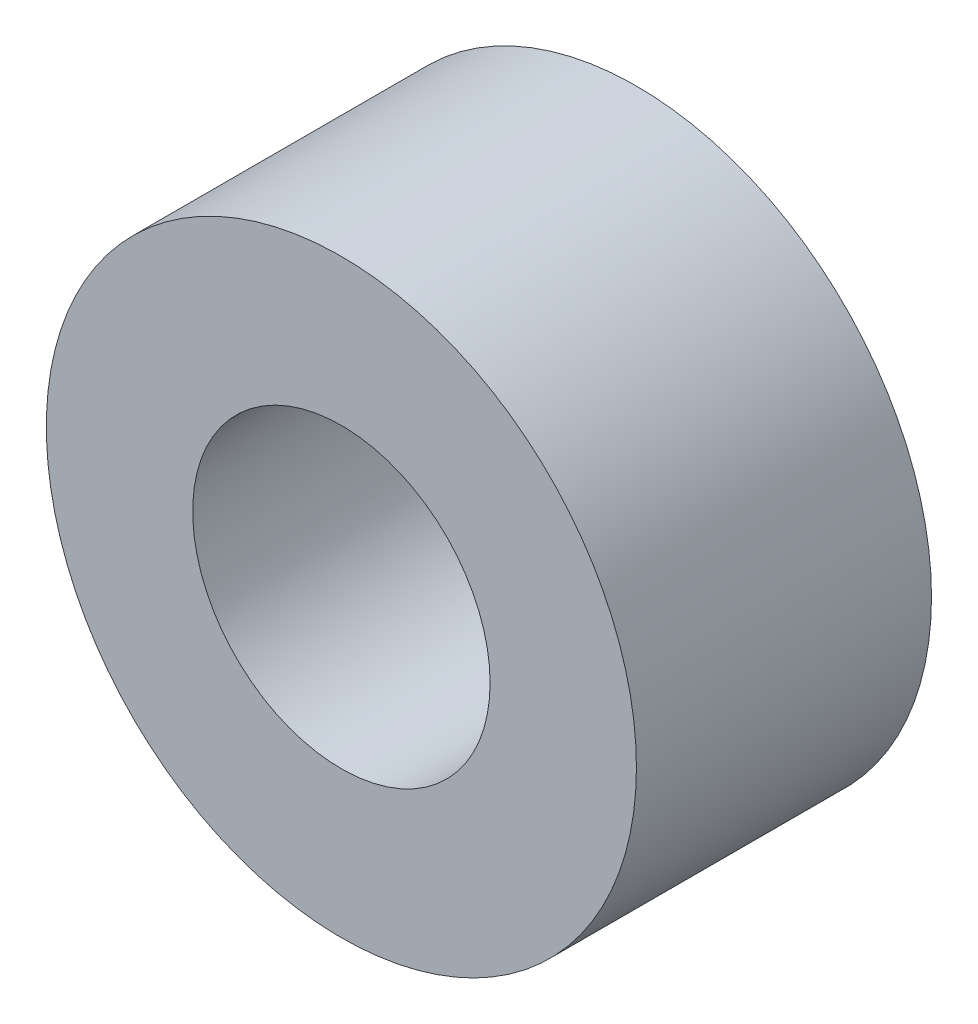
SolidWorks part; units mm, degrees
ref_plane "Front Plane" through (0, 0, 0) normal (0, 0, 1) x (1, 0, 0)
ref_plane "Top Plane" through (0, 0, 0) normal (0, 1, 0) x (1, 0, 0)
ref_plane "Right Plane" through (0, 0, 0) normal (1, 0, 0) x (0, 0, -1)
sketch "Sketch1" plane through (0, 0, 0) normal (0, 0, 1) x (1, 0, 0)
  circle A0 centre (0, 0) radius 6.35
  circle A1 centre (0, 0) radius 3.2004
  dimension "OD" = 12.7
  dimension "ID" = 6.4008
extrude "Extrude1" add sketch "Sketch1" along normal mid plane 6.35
sketch "Sketch2" plane through (0, 0, 0) normal (1, 0, 0) x (0, 0, -1)
  line L0 (-3.175, -3.2004) -> (3.175, -3.2004) construction
  line L3 (3.175, 3.2004) -> (-3.175, 3.2004) construction
  line L5 (-3.175, -3.2004) -> (3.175, -3.2004)
  line L6 (3.175, 3.2004) -> (-3.175, 3.2004)
sketch "Sketch4" plane through (0, 0, 3.175) normal (0, 0, 1) x (1, 0, 0)
  line L0 (0, 0) -> (-2.263, 2.263)
  line L1 (0, -6.985) -> (0, 6.985) construction
  circle A0 centre (0, 0) radius 3.2004 construction
  dimension "D1" = 45
